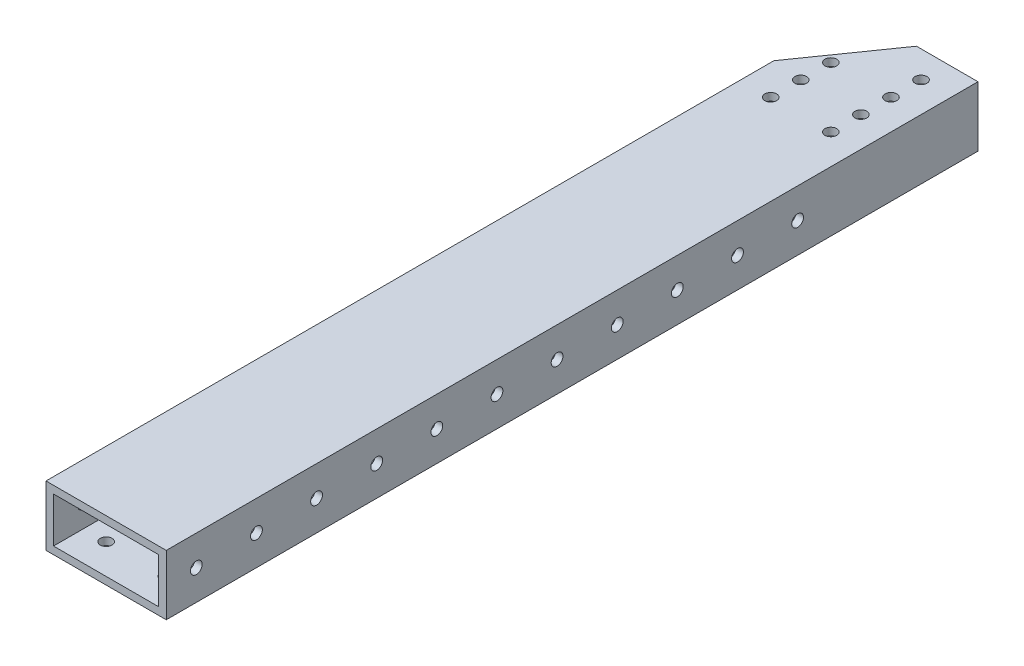
SolidWorks part; units mm, degrees
material "6061-T6 (SS)"
ref_plane "Front Plane" through (0, 0, 0) normal (0, 0, 1) x (1, 0, 0)
ref_plane "Top Plane" through (0, 0, 0) normal (0, 1, 0) x (1, 0, 0)
ref_plane "Right Plane" through (0, 0, 0) normal (1, 0, 0) x (0, 0, -1)
sketch "Sketch1" plane through (0, 0, 0) normal (0, 1, 0) x (1, 0, 0)
  line L1 (0, 0) -> (50.8, 0)
  line L2 (0, 0) -> (0, 342.9)
  line L3 (0, 342.9) -> (50.8, 342.9)
  line L4 (50.8, 0) -> (50.8, 342.9)
  dimension "D1" = 50.8
  dimension "D2" = 342.9
extrude "Boss-Extrude1" add sketch "Sketch1" along normal blind 25.4
shell "Shell1" thickness 3.175
sketch "Sketch2" plane through (0, 0, 0) normal (-1, 0, 0) x (0, 0, 1)
  line L0 (0, 12.7) -> (-342.9, 12.7) construction
  line L1 (0, 25.4) -> (0, 0) construction
  line L2 (-342.9, 25.4) -> (-342.9, 0) construction
  circle A0 centre (-12.7, 12.7) radius 2.4892
  circle A1 centre (-38.1, 12.7) radius 2.4892
  circle A2 centre (-63.5, 12.7) radius 2.4892
  circle A3 centre (-88.9, 12.7) radius 2.4892
  circle A4 centre (-114.3, 12.7) radius 2.4892
  circle A5 centre (-139.7, 12.7) radius 2.4892
  circle A6 centre (-165.1, 12.7) radius 2.4892
  circle A7 centre (-190.5, 12.7) radius 2.4892
  circle A8 centre (-215.9, 12.7) radius 2.4892
  circle A9 centre (-241.3, 12.7) radius 2.4892
  circle A10 centre (-266.7, 12.7) radius 2.4892
  dimension "D1" = 4.9784
  dimension "D2" = 12.7
  dimension "D3" = 25.4
  dimension "D4" = 11
extrude "Cut-Extrude1" cut sketch "Sketch2" against normal through all
sketch "Sketch3" plane through (0, 25.4, 0) normal (0, 1, 0) x (1, 0, 0)
  circle A0 centre (12.7, 293.4246) radius 2.4892 construction
  circle A1 centre (38.1, 293.4246) radius 2.4892 construction
  circle A2 centre (38.1, 306.1246) radius 2.4892 construction
  circle A3 centre (12.7, 306.1246) radius 2.4892 construction
  circle A4 centre (12.7, 318.8246) radius 2.4892 construction
  circle A5 centre (38.1, 318.8246) radius 2.4892 construction
  circle A6 centre (38.1, 331.5246) radius 2.4892 construction
  circle A7 centre (12.7, 331.5246) radius 2.4892 construction
  circle A8 centre (12.7, 293.4246) radius 2.4892
  circle A9 centre (38.1, 293.4246) radius 2.4892
  circle A10 centre (38.1, 306.1246) radius 2.4892
  circle A11 centre (12.7, 306.1246) radius 2.4892
  circle A12 centre (12.7, 318.8246) radius 2.4892
  circle A13 centre (38.1, 318.8246) radius 2.4892
  circle A14 centre (38.1, 331.5246) radius 2.4892
  circle A15 centre (12.7, 331.5246) radius 2.4892
extrude "Cut-Extrude2" cut sketch "Sketch3" against normal through all
sketch "Sketch4" plane through (0, 0, 0) normal (0, -1, 0) x (1, 0, 0)
  circle A0 centre (38.1, -12.7) radius 2.4892 construction
  circle A2 centre (12.7, -12.7) radius 2.4892 construction
  circle A3 centre (12.7, -25.4) radius 2.4892 construction
  circle A5 centre (38.1, -25.4) radius 2.4892 construction
  circle A6 centre (38.1, -38.1) radius 2.4892 construction
  circle A8 centre (12.7, -38.1) radius 2.4892 construction
  circle A9 centre (12.7, -50.8) radius 2.4892 construction
  circle A11 centre (38.1, -50.8) radius 2.4892 construction
  circle A12 centre (38.1, -63.5) radius 2.4892 construction
  circle A14 centre (12.7, -63.5) radius 2.4892 construction
  circle A15 centre (38.1, -12.7) radius 2.4892
  circle A17 centre (12.7, -12.7) radius 2.4892
  circle A18 centre (12.7, -25.4) radius 2.4892
  circle A20 centre (38.1, -25.4) radius 2.4892
  circle A21 centre (38.1, -38.1) radius 2.4892
  circle A23 centre (12.7, -38.1) radius 2.4892
  circle A24 centre (12.7, -50.8) radius 2.4892
  circle A26 centre (38.1, -50.8) radius 2.4892
  circle A27 centre (38.1, -63.5) radius 2.4892
  circle A29 centre (12.7, -63.5) radius 2.4892
extrude "Cut-Extrude3" cut sketch "Sketch4" against normal up to next
sketch "Sketch6" plane through (0, 0, 0) normal (0, -1, 0) x (1, 0, 0)
  line L0 (0, -342.9) -> (0, 0) construction
  line L1 (50.8, -342.9) -> (0, -342.9) construction
  line L2 (0, -342.9) -> (0, 0)
  line L3 (50.8, -342.9) -> (0, -342.9)
  line L4 (24.8061, -342.9) -> (0, -307.4732)
  circle M19 centre (12.7, -331.5246) radius 2.4892
  line M22 (0, -342.9) -> (50.8, -342.9)
  dimension "D1" = 35
  dimension "D2" = 20.32
extrude "Cut-Extrude5" cut sketch "Sketch6" against normal through all contours L4 L2 M22 M19
